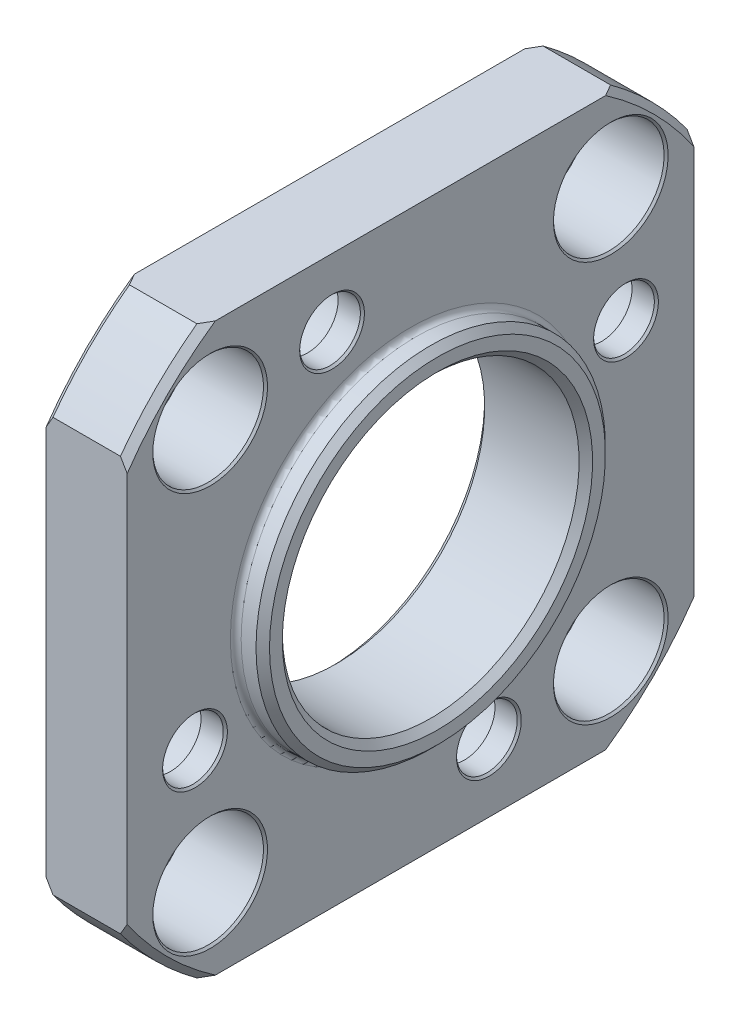
SolidWorks part; units mm, degrees
material "Простая углеродистая сталь"
ref_plane "Спереди  XY" through (0, 0, 0) normal (0, 0, 1) x (1, 0, 0)
ref_plane "Сверху  XZ" through (0, 0, 0) normal (0, 1, 0) x (1, 0, 0)
ref_plane "Справа  ZY" through (0, 0, 0) normal (1, 0, 0) x (0, 0, -1)
sketch "Эскиз1" plane through (0, 0, 0) normal (0, 0, 1) x (1, 0, 0)
  line L0 (0, 0) -> (8, 0) construction
  line L1 (7.5, 11) -> (0.5, 11)
  line L2 (0, 11.5) -> (0, 25.5)
  line L3 (0.5, 26) -> (5.5, 26)
  line L4 (6, 25.5) -> (6, 13.35)
  line L5 (6.4, 12.95) -> (7.5, 12.95)
  line L6 (8, 12.45) -> (8, 11.5)
  line L7 (0.5, 11) -> (0, 11.5)
  line L8 (8, 11.5) -> (7.5, 11)
  line L9 (7.5, 12.95) -> (8, 12.45)
  line L10 (0, 25.5) -> (0.5, 26)
  line L11 (5.5, 26) -> (6, 25.5)
  arc A0 (6, 13.35) -> (6.4, 12.95) centre (6.4, 13.35) ccw
  point P3 (8, 11)
  point P4 (0, 11)
  point P6 (0, 26)
  point P7 (6, 26)
  point P8 (0, 0)
  point P9 (8, 12.95)
  point P10 (0, 0)
  dimension "D6" = 0.4
  dimension "D1" = 8
  dimension "D2" = 11
  dimension "D3" = 26
  dimension "D4" = 12.95
  dimension "D5" = 2
revolve "Повернуть1" add sketch "Эскиз1" angle 360 about L0
sketch "Эскиз2" plane through (0, 0, 0) normal (-1, 0, 0) x (0, 0, 1)
  line L0 (0, 0) -> (0, 21) construction
  line L1 (-15.3297, 21) -> (15.3297, 21)
  line L2 (21, 15.3297) -> (21, -15.3297)
  line L3 (0, 0) -> (21, 0) construction
  line L4 (15.3297, -21) -> (-15.3297, -21)
  line L5 (0, 0) -> (0, -21) construction
  line L6 (-21, -15.3297) -> (-21, 15.3297)
  line L7 (0, 0) -> (-21, 0) construction
  circle A0 centre (0, 0) radius 26 construction
  arc A1 (-21, 15.3297) -> (-21, -15.3297) centre (0, 0) ccw
  arc A3 (-15.3297, -21) -> (15.3297, -21) centre (0, 0) ccw
  arc A4 (21, -15.3297) -> (21, 15.3297) centre (0, 0) ccw
  arc A5 (15.3297, 21) -> (-15.3297, 21) centre (0, 0) ccw
  point P19 (0, 0)
  dimension "D1" = 21
  dimension "D2" = 4
extrude "Вырез-Вытянуть1" cut sketch "Эскиз2" against normal up to next
hole_wizard "Цековка для винта с внутренним шестигранником M41" positions "Эскиз3" profile "Эскиз4" counterbore size "M4" standard "Ansi Metric" end condition up to next
sketch "Эскиз3" plane through (0, 0, 0) normal (-1, 0, 0) x (0, 0, 1)
  line L0 (0, 0) -> (0, 21) construction
  line L1 (-14.4655, 21) -> (14.4655, 21) construction
  line L3 (-5.8143, -15.9748) -> (5.8143, 15.9748) construction
  line L5 (-15.9748, 5.8143) -> (15.9748, -5.8143) construction
  point P0 (5.8143, 15.9748)
  point P2 (-15.9748, 5.8143)
  point P4 (-5.8143, -15.9748)
  point P6 (15.9748, -5.8143)
  dimension "D1" = 34
  dimension "D2" = 20
  dimension "D3" = 90
sketch "Эскиз4" plane through (0, 15.9748, 5.8143) normal (0, 1, 0) x (0, 0, 1)
  line L0 (0, 0) -> (0, 6)
  line L1 (2.25, 5.85) -> (2.4, 6)
  line L2 (3.7, 4.2) -> (2.25, 4.2)
  line L3 (2.25, 4.2) -> (2.25, 5.85)
  line L5 (3.7, 4.2) -> (3.7, 0.15)
  line L6 (3.7, 0.15) -> (3.85, 0)
  line L7 (3.85, 0) -> (0, 0)
  line L8 (-3.7, 0.15) -> (-3.85, 0) construction
  line L11 (0, -6.35) -> (0, 107.95) construction
  line L12 (2.4, 6) -> (0, 6)
  line L13 (-2.25, 5.85) -> (-2.4, 6) construction
  dimension "Диаметр сквозного отверстия" = 4.5
  dimension "Глубина сквозного отверстия" = 6
  dimension "Диаметр цековки" = 7.4
  dimension "Глубина цековки" = 4.2
  dimension "Диаметр передней зенковки" = 7.7
  dimension "Угол передней зенковки" = 90
  dimension "Диаметр задней зенковки" = 4.8
  dimension "Угол задней зенковки" = 90
hole_wizard "Диаметр отверстия Ø8.2 (8.2)1" positions "Эскиз5" profile "Эскиз6" hole size "Ø8.2" standard "Ansi Metric" end condition up to next
sketch "Эскиз5" plane through (0, 0, 0) normal (-1, 0, 0) x (0, 0, 1)
  line L0 (0, 0) -> (0, 21) construction
  line L1 (-14.4655, 21) -> (14.4655, 21) construction
  line L3 (-14.8492, 14.8492) -> (14.8492, -14.8492) construction
  line L5 (-14.8492, -14.8492) -> (14.8492, 14.8492) construction
  point P0 (-14.8492, 14.8492)
  point P2 (14.8492, 14.8492)
  point P4 (14.8492, -14.8492)
  point P6 (-14.8492, -14.8492)
  dimension "D1" = 45
  dimension "D2" = 90
  dimension "D3" = 42
sketch "Эскиз6" plane through (0, 14.8492, -14.8492) normal (0, 1, 0) x (0, 0, 1)
  line L0 (0, 0) -> (0, 6)
  line L1 (0, 6) -> (4.25, 6)
  line L2 (4.1, 5.85) -> (4.1, 0.15)
  line L3 (4.1, 0.15) -> (4.25, 0)
  line L5 (4.25, 0) -> (0, 0)
  line L6 (-4.1, 0.15) -> (-4.25, 0) construction
  line L7 (4.25, 6) -> (4.1, 5.85)
  line L8 (-4.25, 6) -> (-4.1, 5.85) construction
  line L11 (0, -6.35) -> (0, 107.95) construction
  dimension "Диаметр сквозного отверстия" = 8.2
  dimension "Глубина сквозного отверстия" = 6
  dimension "Диаметр передней зенковки" = 8.5
  dimension "Угол передней зенковки" = 90
  dimension "Диаметр задней зенковки" = 8.5
  dimension "Угол задней зенковки" = 90
